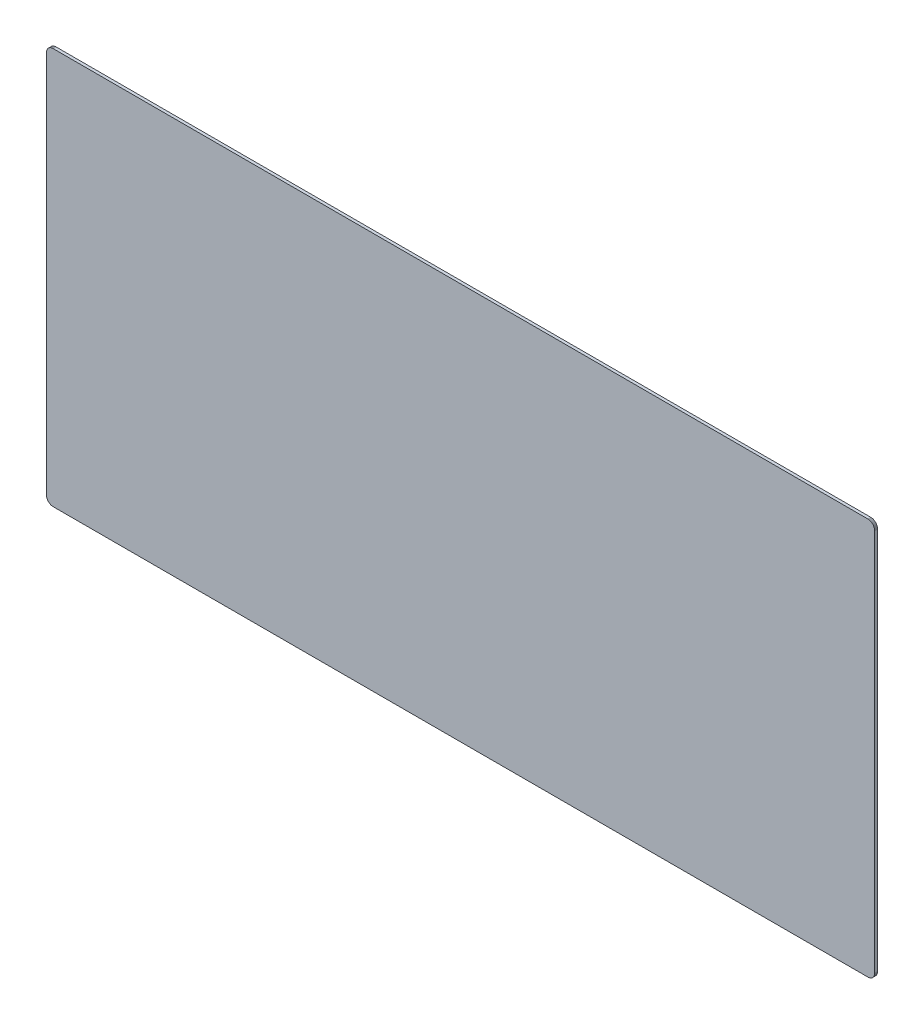
SolidWorks part; units mm, degrees
ref_plane "Front Plane" through (0, 0, 0) normal (0, 0, 1) x (1, 0, 0)
ref_plane "Top Plane" through (0, 0, 0) normal (0, 1, 0) x (1, 0, 0)
ref_plane "Right Plane" through (0, 0, 0) normal (1, 0, 0) x (0, 0, -1)
sketch "Model" plane through (0, 0, 0) normal (0, 0, 1) x (1, 0, 0)
  line L0 (364.568, 176.294) -> (364.804, 176.284)
  line L1 (364.804, 176.284) -> (365.037, 176.258)
  line L2 (365.037, 176.258) -> (365.27, 176.211)
  line L3 (365.27, 176.211) -> (365.495, 176.148)
  line L4 (365.495, 176.148) -> (365.718, 176.065)
  line L5 (365.718, 176.065) -> (365.933, 175.967)
  line L6 (365.933, 175.967) -> (366.134, 175.852)
  line L7 (366.134, 175.852) -> (366.332, 175.722)
  line L8 (366.332, 175.722) -> (366.518, 175.576)
  line L9 (366.518, 175.576) -> (366.688, 175.416)
  line L10 (366.688, 175.416) -> (366.85, 175.242)
  line L11 (366.85, 175.242) -> (366.995, 175.058)
  line L12 (366.995, 175.058) -> (367.125, 174.862)
  line L13 (367.125, 174.862) -> (367.242, 174.655)
  line L14 (367.242, 174.655) -> (367.34, 174.442)
  line L15 (367.34, 174.442) -> (367.422, 174.221)
  line L16 (367.422, 174.221) -> (367.485, 173.994)
  line L17 (367.485, 173.994) -> (367.531, 173.764)
  line L18 (367.531, 173.764) -> (367.559, 173.53)
  line L19 (367.559, 173.53) -> (367.57, 173.294)
  line L20 (367.57, 173.294) -> (367.57, 3.2728)
  line L21 (367.57, 3.2728) -> (367.559, 3.0372)
  line L22 (367.559, 3.0372) -> (367.531, 2.8029)
  line L23 (367.531, 2.8029) -> (367.485, 2.5728)
  line L24 (367.485, 2.5728) -> (367.422, 2.3454)
  line L25 (367.422, 2.3454) -> (367.34, 2.1249)
  line L26 (367.34, 2.1249) -> (367.242, 1.9113)
  line L27 (367.242, 1.9113) -> (367.125, 1.706)
  line L28 (367.125, 1.706) -> (366.995, 1.509)
  line L29 (366.995, 1.509) -> (366.85, 1.3243)
  line L30 (366.85, 1.3243) -> (366.688, 1.152)
  line L31 (366.688, 1.152) -> (366.518, 0.9908)
  line L32 (366.518, 0.9908) -> (366.332, 0.8447)
  line L33 (366.332, 0.8447) -> (366.134, 0.7152)
  line L34 (366.134, 0.7152) -> (365.933, 0.5994)
  line L35 (365.933, 0.5994) -> (365.718, 0.5016)
  line L36 (365.718, 0.5016) -> (365.495, 0.4189)
  line L37 (365.495, 0.4189) -> (365.27, 0.3555)
  line L38 (365.27, 0.3555) -> (365.037, 0.3101)
  line L39 (365.037, 0.3101) -> (364.804, 0.2825)
  line L40 (364.804, 0.2825) -> (364.568, 0.2729)
  line L41 (364.568, 0.2729) -> (3.0951, 0.2729)
  line L42 (3.0951, 0.2729) -> (2.8594, 0.2825)
  line L43 (2.8594, 0.2825) -> (2.6252, 0.3101)
  line L44 (2.6252, 0.3101) -> (2.395, 0.3555)
  line L45 (2.395, 0.3555) -> (2.1677, 0.4189)
  line L46 (2.1677, 0.4189) -> (1.9472, 0.5016)
  line L47 (1.9472, 0.5016) -> (1.7336, 0.5994)
  line L48 (1.7336, 0.5994) -> (1.5269, 0.7152)
  line L49 (1.5269, 0.7152) -> (1.3312, 0.8447)
  line L50 (1.3312, 0.8447) -> (1.1465, 0.9908)
  line L51 (1.1465, 0.9908) -> (0.9729, 1.152)
  line L52 (0.9729, 1.152) -> (0.813, 1.3243)
  line L53 (0.813, 1.3243) -> (0.667, 1.509)
  line L54 (0.667, 1.509) -> (0.5374, 1.706)
  line L55 (0.5374, 1.706) -> (0.4217, 1.9113)
  line L56 (0.4217, 1.9113) -> (0.3238, 2.1249)
  line L57 (0.3238, 2.1249) -> (0.2412, 2.3454)
  line L58 (0.2412, 2.3454) -> (0.1778, 2.5728)
  line L59 (0.1778, 2.5728) -> (0.1309, 2.8029)
  line L60 (0.1309, 2.8029) -> (0.1047, 3.0372)
  line L61 (0.1047, 3.0372) -> (0.0951, 3.2728)
  line L62 (0.0951, 3.2728) -> (0.0951, 173.294)
  line L63 (0.0951, 173.294) -> (0.1047, 173.53)
  line L64 (0.1047, 173.53) -> (0.1309, 173.764)
  line L65 (0.1309, 173.764) -> (0.1778, 173.994)
  line L66 (0.1778, 173.994) -> (0.2412, 174.221)
  line L67 (0.2412, 174.221) -> (0.3238, 174.442)
  line L68 (0.3238, 174.442) -> (0.4217, 174.655)
  line L69 (0.4217, 174.655) -> (0.5374, 174.862)
  line L70 (0.5374, 174.862) -> (0.667, 175.058)
  line L71 (0.667, 175.058) -> (0.813, 175.242)
  line L72 (0.813, 175.242) -> (0.9729, 175.416)
  line L73 (0.9729, 175.416) -> (1.1465, 175.576)
  line L74 (1.1465, 175.576) -> (1.3312, 175.722)
  line L75 (1.3312, 175.722) -> (1.5269, 175.852)
  line L76 (1.5269, 175.852) -> (1.7336, 175.967)
  line L77 (1.7336, 175.967) -> (1.9472, 176.065)
  line L78 (1.9472, 176.065) -> (2.1677, 176.148)
  line L79 (2.1677, 176.148) -> (2.395, 176.211)
  line L80 (2.395, 176.211) -> (2.6252, 176.258)
  line L81 (2.6252, 176.258) -> (2.8594, 176.284)
  line L82 (2.8594, 176.284) -> (3.0951, 176.294)
  line L83 (3.0951, 176.294) -> (364.568, 176.294)
  line L84 (3.7703, 5.271) -> (3.4782, 5.1222) construction
  line L85 (3.4782, 5.1222) -> (3.2453, 4.8907) construction
  line L86 (3.2453, 4.8907) -> (3.0951, 4.5972) construction
  line L87 (3.0951, 4.5972) -> (3.0441, 4.2719) construction
  line L88 (3.0441, 4.2719) -> (3.0951, 3.9481) construction
  line L89 (3.0951, 3.9481) -> (3.2453, 3.6559) construction
  line L90 (3.2453, 3.6559) -> (3.4782, 3.423) construction
  line L91 (3.4782, 3.423) -> (3.7703, 3.2742) construction
  line L92 (3.7703, 3.2742) -> (4.0955, 3.2218) construction
  line L93 (4.0955, 3.2218) -> (4.4193, 3.2742) construction
  line L94 (4.4193, 3.2742) -> (4.7129, 3.423) construction
  line L95 (4.7129, 3.423) -> (4.9444, 3.6559) construction
  line L96 (4.9444, 3.6559) -> (5.0932, 3.9481) construction
  line L97 (5.0932, 3.9481) -> (5.1456, 4.2719) construction
  line L98 (5.1456, 4.2719) -> (5.0932, 4.5972) construction
  line L99 (5.0932, 4.5972) -> (4.9444, 4.8907) construction
  line L100 (4.9444, 4.8907) -> (4.7129, 5.1222) construction
  line L101 (4.7129, 5.1222) -> (4.4193, 5.271) construction
  line L102 (4.4193, 5.271) -> (4.0955, 5.322) construction
  line L103 (4.0955, 5.322) -> (3.7703, 5.271) construction
  line L104 (75.6652, 5.271) -> (75.3731, 5.1222) construction
  line L105 (75.3731, 5.1222) -> (75.1403, 4.8907) construction
  line L106 (75.1403, 4.8907) -> (74.9914, 4.5972) construction
  line L107 (74.9914, 4.5972) -> (74.9392, 4.2719) construction
  line L108 (74.9392, 4.2719) -> (74.9914, 3.9481) construction
  line L109 (74.9914, 3.9481) -> (75.1403, 3.6559) construction
  line L110 (75.1403, 3.6559) -> (75.3731, 3.423) construction
  line L111 (75.3731, 3.423) -> (75.6652, 3.2742) construction
  line L112 (75.6652, 3.2742) -> (75.989, 3.2218) construction
  line L113 (75.989, 3.2218) -> (76.3143, 3.2742) construction
  line L114 (76.3143, 3.2742) -> (76.6064, 3.423) construction
  line L115 (76.6064, 3.423) -> (76.8396, 3.6559) construction
  line L116 (76.8396, 3.6559) -> (76.9881, 3.9481) construction
  line L117 (76.9881, 3.9481) -> (77.0393, 4.2719) construction
  line L118 (77.0393, 4.2719) -> (76.9881, 4.5972) construction
  line L119 (76.9881, 4.5972) -> (76.8396, 4.8907) construction
  line L120 (76.8396, 4.8907) -> (76.6064, 5.1222) construction
  line L121 (76.6064, 5.1222) -> (76.3143, 5.271) construction
  line L122 (76.3143, 5.271) -> (75.989, 5.322) construction
  line L123 (75.989, 5.322) -> (75.6652, 5.271) construction
  line L124 (147.559, 5.271) -> (147.267, 5.1222) construction
  line L125 (147.267, 5.1222) -> (147.034, 4.8907) construction
  line L126 (147.034, 4.8907) -> (146.885, 4.5972) construction
  line L127 (146.885, 4.5972) -> (146.834, 4.2719) construction
  line L128 (146.834, 4.2719) -> (146.885, 3.9481) construction
  line L129 (146.885, 3.9481) -> (147.034, 3.6559) construction
  line L130 (147.034, 3.6559) -> (147.267, 3.423) construction
  line L131 (147.267, 3.423) -> (147.559, 3.2742) construction
  line L132 (147.559, 3.2742) -> (147.884, 3.2218) construction
  line L133 (147.884, 3.2218) -> (148.208, 3.2742) construction
  line L134 (148.208, 3.2742) -> (148.501, 3.423) construction
  line L135 (148.501, 3.423) -> (148.733, 3.6559) construction
  line L136 (148.733, 3.6559) -> (148.883, 3.9481) construction
  line L137 (148.883, 3.9481) -> (148.934, 4.2719) construction
  line L138 (148.934, 4.2719) -> (148.883, 4.5972) construction
  line L139 (148.883, 4.5972) -> (148.733, 4.8907) construction
  line L140 (148.733, 4.8907) -> (148.501, 5.1222) construction
  line L141 (148.501, 5.1222) -> (148.208, 5.271) construction
  line L142 (148.208, 5.271) -> (147.884, 5.322) construction
  line L143 (147.884, 5.322) -> (147.559, 5.271) construction
  line L144 (219.454, 5.271) -> (219.162, 5.1222) construction
  line L145 (219.162, 5.1222) -> (218.929, 4.8907) construction
  line L146 (218.929, 4.8907) -> (218.78, 4.5972) construction
  line L147 (218.78, 4.5972) -> (218.729, 4.2719) construction
  line L148 (218.729, 4.2719) -> (218.78, 3.9481) construction
  line L149 (218.78, 3.9481) -> (218.929, 3.6559) construction
  line L150 (218.929, 3.6559) -> (219.162, 3.423) construction
  line L151 (219.162, 3.423) -> (219.454, 3.2742) construction
  line L152 (219.454, 3.2742) -> (219.779, 3.2218) construction
  line L153 (219.779, 3.2218) -> (220.103, 3.2742) construction
  line L154 (220.103, 3.2742) -> (220.396, 3.423) construction
  line L155 (220.396, 3.423) -> (220.628, 3.6559) construction
  line L156 (220.628, 3.6559) -> (220.777, 3.9481) construction
  line L157 (220.777, 3.9481) -> (220.829, 4.2719) construction
  line L158 (220.829, 4.2719) -> (220.777, 4.5972) construction
  line L159 (220.777, 4.5972) -> (220.628, 4.8907) construction
  line L160 (220.628, 4.8907) -> (220.396, 5.1222) construction
  line L161 (220.396, 5.1222) -> (220.103, 5.271) construction
  line L162 (220.103, 5.271) -> (219.779, 5.322) construction
  line L163 (219.779, 5.322) -> (219.454, 5.271) construction
  line L164 (291.349, 5.271) -> (291.057, 5.1222) construction
  line L165 (291.057, 5.1222) -> (290.824, 4.8907) construction
  line L166 (290.824, 4.8907) -> (290.675, 4.5972) construction
  line L167 (290.675, 4.5972) -> (290.624, 4.2719) construction
  line L168 (290.624, 4.2719) -> (290.675, 3.9481) construction
  line L169 (290.675, 3.9481) -> (290.824, 3.6559) construction
  line L170 (290.824, 3.6559) -> (291.057, 3.423) construction
  line L171 (291.057, 3.423) -> (291.349, 3.2742) construction
  line L172 (291.349, 3.2742) -> (291.673, 3.2218) construction
  line L173 (291.673, 3.2218) -> (291.998, 3.2742) construction
  line L174 (291.998, 3.2742) -> (292.29, 3.423) construction
  line L175 (292.29, 3.423) -> (292.523, 3.6559) construction
  line L176 (292.523, 3.6559) -> (292.672, 3.9481) construction
  line L177 (292.672, 3.9481) -> (292.723, 4.2719) construction
  line L178 (292.723, 4.2719) -> (292.672, 4.5972) construction
  line L179 (292.672, 4.5972) -> (292.523, 4.8907) construction
  line L180 (292.523, 4.8907) -> (292.29, 5.1222) construction
  line L181 (292.29, 5.1222) -> (291.998, 5.271) construction
  line L182 (291.998, 5.271) -> (291.673, 5.322) construction
  line L183 (291.673, 5.322) -> (291.349, 5.271) construction
  line L184 (363.245, 5.271) -> (362.952, 5.1222) construction
  line L185 (362.952, 5.1222) -> (362.719, 4.8907) construction
  line L186 (362.719, 4.8907) -> (362.571, 4.5972) construction
  line L187 (362.571, 4.5972) -> (362.518, 4.2719) construction
  line L188 (362.518, 4.2719) -> (362.571, 3.9481) construction
  line L189 (362.571, 3.9481) -> (362.719, 3.6559) construction
  line L190 (362.719, 3.6559) -> (362.952, 3.423) construction
  line L191 (362.952, 3.423) -> (363.245, 3.2742) construction
  line L192 (363.245, 3.2742) -> (363.569, 3.2218) construction
  line L193 (363.569, 3.2218) -> (363.894, 3.2742) construction
  line L194 (363.894, 3.2742) -> (364.187, 3.423) construction
  line L195 (364.187, 3.423) -> (364.419, 3.6559) construction
  line L196 (364.419, 3.6559) -> (364.568, 3.9481) construction
  line L197 (364.568, 3.9481) -> (364.617, 4.2719) construction
  line L198 (364.617, 4.2719) -> (364.568, 4.5972) construction
  line L199 (364.568, 4.5972) -> (364.419, 4.8907) construction
  line L200 (364.419, 4.8907) -> (364.187, 5.1222) construction
  line L201 (364.187, 5.1222) -> (363.894, 5.271) construction
  line L202 (363.894, 5.271) -> (363.569, 5.322) construction
  line L203 (363.569, 5.322) -> (363.245, 5.271) construction
  line L204 (3.7703, 89.2817) -> (3.4782, 89.1328) construction
  line L205 (3.4782, 89.1328) -> (3.2453, 88.9) construction
  line L206 (3.2453, 88.9) -> (3.0951, 88.6079) construction
  line L207 (3.0951, 88.6079) -> (3.0441, 88.284) construction
  line L208 (3.0441, 88.284) -> (3.0951, 87.9588) construction
  line L209 (3.0951, 87.9588) -> (3.2453, 87.6667) construction
  line L210 (3.2453, 87.6667) -> (3.4782, 87.4339) construction
  line L211 (3.4782, 87.4339) -> (3.7703, 87.285) construction
  line L212 (3.7703, 87.285) -> (4.0955, 87.2338) construction
  line L213 (4.0955, 87.2338) -> (4.4193, 87.285) construction
  line L214 (4.4193, 87.285) -> (4.7129, 87.4339) construction
  line L215 (4.7129, 87.4339) -> (4.9444, 87.6667) construction
  line L216 (4.9444, 87.6667) -> (5.0932, 87.9588) construction
  line L217 (5.0932, 87.9588) -> (5.1456, 88.284) construction
  line L218 (5.1456, 88.284) -> (5.0932, 88.6079) construction
  line L219 (5.0932, 88.6079) -> (4.9444, 88.9) construction
  line L220 (4.9444, 88.9) -> (4.7129, 89.1328) construction
  line L221 (4.7129, 89.1328) -> (4.4193, 89.2817) construction
  line L222 (4.4193, 89.2817) -> (4.0955, 89.3339) construction
  line L223 (4.0955, 89.3339) -> (3.7703, 89.2817) construction
  line L224 (363.245, 89.2817) -> (362.952, 89.1328) construction
  line L225 (362.952, 89.1328) -> (362.719, 88.9) construction
  line L226 (362.719, 88.9) -> (362.571, 88.6079) construction
  line L227 (362.571, 88.6079) -> (362.518, 88.284) construction
  line L228 (362.518, 88.284) -> (362.571, 87.9588) construction
  line L229 (362.571, 87.9588) -> (362.719, 87.6667) construction
  line L230 (362.719, 87.6667) -> (362.952, 87.4339) construction
  line L231 (362.952, 87.4339) -> (363.245, 87.285) construction
  line L232 (363.245, 87.285) -> (363.569, 87.2338) construction
  line L233 (363.569, 87.2338) -> (363.894, 87.285) construction
  line L234 (363.894, 87.285) -> (364.187, 87.4339) construction
  line L235 (364.187, 87.4339) -> (364.419, 87.6667) construction
  line L236 (364.419, 87.6667) -> (364.568, 87.9588) construction
  line L237 (364.568, 87.9588) -> (364.617, 88.284) construction
  line L238 (364.617, 88.284) -> (364.568, 88.6079) construction
  line L239 (364.568, 88.6079) -> (364.419, 88.9) construction
  line L240 (364.419, 88.9) -> (364.187, 89.1328) construction
  line L241 (364.187, 89.1328) -> (363.894, 89.2817) construction
  line L242 (363.894, 89.2817) -> (363.569, 89.3339) construction
  line L243 (363.569, 89.3339) -> (363.245, 89.2817) construction
  line L244 (3.7703, 173.294) -> (3.4782, 173.144) construction
  line L245 (3.4782, 173.144) -> (3.2453, 172.911) construction
  line L246 (3.2453, 172.911) -> (3.0951, 172.619) construction
  line L247 (3.0951, 172.619) -> (3.0441, 172.293) construction
  line L248 (3.0441, 172.293) -> (3.0951, 171.97) construction
  line L249 (3.0951, 171.97) -> (3.2453, 171.676) construction
  line L250 (3.2453, 171.676) -> (3.4782, 171.444) construction
  line L251 (3.4782, 171.444) -> (3.7703, 171.296) construction
  line L252 (3.7703, 171.296) -> (4.0955, 171.243) construction
  line L253 (4.0955, 171.243) -> (4.4193, 171.296) construction
  line L254 (4.4193, 171.296) -> (4.7129, 171.444) construction
  line L255 (4.7129, 171.444) -> (4.9444, 171.676) construction
  line L256 (4.9444, 171.676) -> (5.0932, 171.97) construction
  line L257 (5.0932, 171.97) -> (5.1456, 172.293) construction
  line L258 (5.1456, 172.293) -> (5.0932, 172.619) construction
  line L259 (5.0932, 172.619) -> (4.9444, 172.911) construction
  line L260 (4.9444, 172.911) -> (4.7129, 173.144) construction
  line L261 (4.7129, 173.144) -> (4.4193, 173.294) construction
  line L262 (4.4193, 173.294) -> (4.0955, 173.343) construction
  line L263 (4.0955, 173.343) -> (3.7703, 173.294) construction
  line L264 (363.245, 173.294) -> (362.952, 173.144) construction
  line L265 (362.952, 173.144) -> (362.719, 172.911) construction
  line L266 (362.719, 172.911) -> (362.571, 172.619) construction
  line L267 (362.571, 172.619) -> (362.518, 172.293) construction
  line L268 (362.518, 172.293) -> (362.571, 171.97) construction
  line L269 (362.571, 171.97) -> (362.719, 171.676) construction
  line L270 (362.719, 171.676) -> (362.952, 171.444) construction
  line L271 (362.952, 171.444) -> (363.245, 171.296) construction
  line L272 (363.245, 171.296) -> (363.569, 171.243) construction
  line L273 (363.569, 171.243) -> (363.894, 171.296) construction
  line L274 (363.894, 171.296) -> (364.187, 171.444) construction
  line L275 (364.187, 171.444) -> (364.419, 171.676) construction
  line L276 (364.419, 171.676) -> (364.568, 171.97) construction
  line L277 (364.568, 171.97) -> (364.617, 172.293) construction
  line L278 (364.617, 172.293) -> (364.568, 172.619) construction
  line L279 (364.568, 172.619) -> (364.419, 172.911) construction
  line L280 (364.419, 172.911) -> (364.187, 173.144) construction
  line L281 (364.187, 173.144) -> (363.894, 173.294) construction
  line L282 (363.894, 173.294) -> (363.569, 173.343) construction
  line L283 (363.569, 173.343) -> (363.245, 173.294) construction
  line L284 (291.349, 173.294) -> (291.057, 173.144) construction
  line L285 (291.057, 173.144) -> (290.824, 172.911) construction
  line L286 (290.824, 172.911) -> (290.675, 172.619) construction
  line L287 (290.675, 172.619) -> (290.624, 172.293) construction
  line L288 (290.624, 172.293) -> (290.675, 171.97) construction
  line L289 (290.675, 171.97) -> (290.824, 171.676) construction
  line L290 (290.824, 171.676) -> (291.057, 171.444) construction
  line L291 (291.057, 171.444) -> (291.349, 171.296) construction
  line L292 (291.349, 171.296) -> (291.673, 171.243) construction
  line L293 (291.673, 171.243) -> (291.998, 171.296) construction
  line L294 (291.998, 171.296) -> (292.29, 171.444) construction
  line L295 (292.29, 171.444) -> (292.523, 171.676) construction
  line L296 (292.523, 171.676) -> (292.672, 171.97) construction
  line L297 (292.672, 171.97) -> (292.723, 172.293) construction
  line L298 (292.723, 172.293) -> (292.672, 172.619) construction
  line L299 (292.672, 172.619) -> (292.523, 172.911) construction
  line L300 (292.523, 172.911) -> (292.29, 173.144) construction
  line L301 (292.29, 173.144) -> (291.998, 173.294) construction
  line L302 (291.998, 173.294) -> (291.673, 173.343) construction
  line L303 (291.673, 173.343) -> (291.349, 173.294) construction
  line L304 (219.454, 173.294) -> (219.162, 173.144) construction
  line L305 (219.162, 173.144) -> (218.929, 172.911) construction
  line L306 (218.929, 172.911) -> (218.78, 172.619) construction
  line L307 (218.78, 172.619) -> (218.729, 172.293) construction
  line L308 (218.729, 172.293) -> (218.78, 171.97) construction
  line L309 (218.78, 171.97) -> (218.929, 171.676) construction
  line L310 (218.929, 171.676) -> (219.162, 171.444) construction
  line L311 (219.162, 171.444) -> (219.454, 171.296) construction
  line L312 (219.454, 171.296) -> (219.779, 171.243) construction
  line L313 (219.779, 171.243) -> (220.103, 171.296) construction
  line L314 (220.103, 171.296) -> (220.396, 171.444) construction
  line L315 (220.396, 171.444) -> (220.628, 171.676) construction
  line L316 (220.628, 171.676) -> (220.777, 171.97) construction
  line L317 (220.777, 171.97) -> (220.829, 172.293) construction
  line L318 (220.829, 172.293) -> (220.777, 172.619) construction
  line L319 (220.777, 172.619) -> (220.628, 172.911) construction
  line L320 (220.628, 172.911) -> (220.396, 173.144) construction
  line L321 (220.396, 173.144) -> (220.103, 173.294) construction
  line L322 (220.103, 173.294) -> (219.779, 173.343) construction
  line L323 (219.779, 173.343) -> (219.454, 173.294) construction
  line L324 (147.559, 173.294) -> (147.267, 173.144) construction
  line L325 (147.267, 173.144) -> (147.034, 172.911) construction
  line L326 (147.034, 172.911) -> (146.885, 172.619) construction
  line L327 (146.885, 172.619) -> (146.834, 172.293) construction
  line L328 (146.834, 172.293) -> (146.885, 171.97) construction
  line L329 (146.885, 171.97) -> (147.034, 171.676) construction
  line L330 (147.034, 171.676) -> (147.267, 171.444) construction
  line L331 (147.267, 171.444) -> (147.559, 171.296) construction
  line L332 (147.559, 171.296) -> (147.884, 171.243) construction
  line L333 (147.884, 171.243) -> (148.208, 171.296) construction
  line L334 (148.208, 171.296) -> (148.501, 171.444) construction
  line L335 (148.501, 171.444) -> (148.733, 171.676) construction
  line L336 (148.733, 171.676) -> (148.883, 171.97) construction
  line L337 (148.883, 171.97) -> (148.934, 172.293) construction
  line L338 (148.934, 172.293) -> (148.883, 172.619) construction
  line L339 (148.883, 172.619) -> (148.733, 172.911) construction
  line L340 (148.733, 172.911) -> (148.501, 173.144) construction
  line L341 (148.501, 173.144) -> (148.208, 173.294) construction
  line L342 (148.208, 173.294) -> (147.884, 173.343) construction
  line L343 (147.884, 173.343) -> (147.559, 173.294) construction
  line L344 (75.6652, 173.294) -> (75.3731, 173.144) construction
  line L345 (75.3731, 173.144) -> (75.1403, 172.911) construction
  line L346 (75.1403, 172.911) -> (74.9914, 172.619) construction
  line L347 (74.9914, 172.619) -> (74.9392, 172.293) construction
  line L348 (74.9392, 172.293) -> (74.9914, 171.97) construction
  line L349 (74.9914, 171.97) -> (75.1403, 171.676) construction
  line L350 (75.1403, 171.676) -> (75.3731, 171.444) construction
  line L351 (75.3731, 171.444) -> (75.6652, 171.296) construction
  line L352 (75.6652, 171.296) -> (75.989, 171.243) construction
  line L353 (75.989, 171.243) -> (76.3143, 171.296) construction
  line L354 (76.3143, 171.296) -> (76.6064, 171.444) construction
  line L355 (76.6064, 171.444) -> (76.8396, 171.676) construction
  line L356 (76.8396, 171.676) -> (76.9881, 171.97) construction
  line L357 (76.9881, 171.97) -> (77.0393, 172.293) construction
  line L358 (77.0393, 172.293) -> (76.9881, 172.619) construction
  line L359 (76.9881, 172.619) -> (76.8396, 172.911) construction
  line L360 (76.8396, 172.911) -> (76.6064, 173.144) construction
  line L361 (76.6064, 173.144) -> (76.3143, 173.294) construction
  line L362 (76.3143, 173.294) -> (75.989, 173.343) construction
  line L363 (75.989, 173.343) -> (75.6652, 173.294) construction
extrude "凸台-拉伸1" add sketch "Model" along normal blind 1.3
